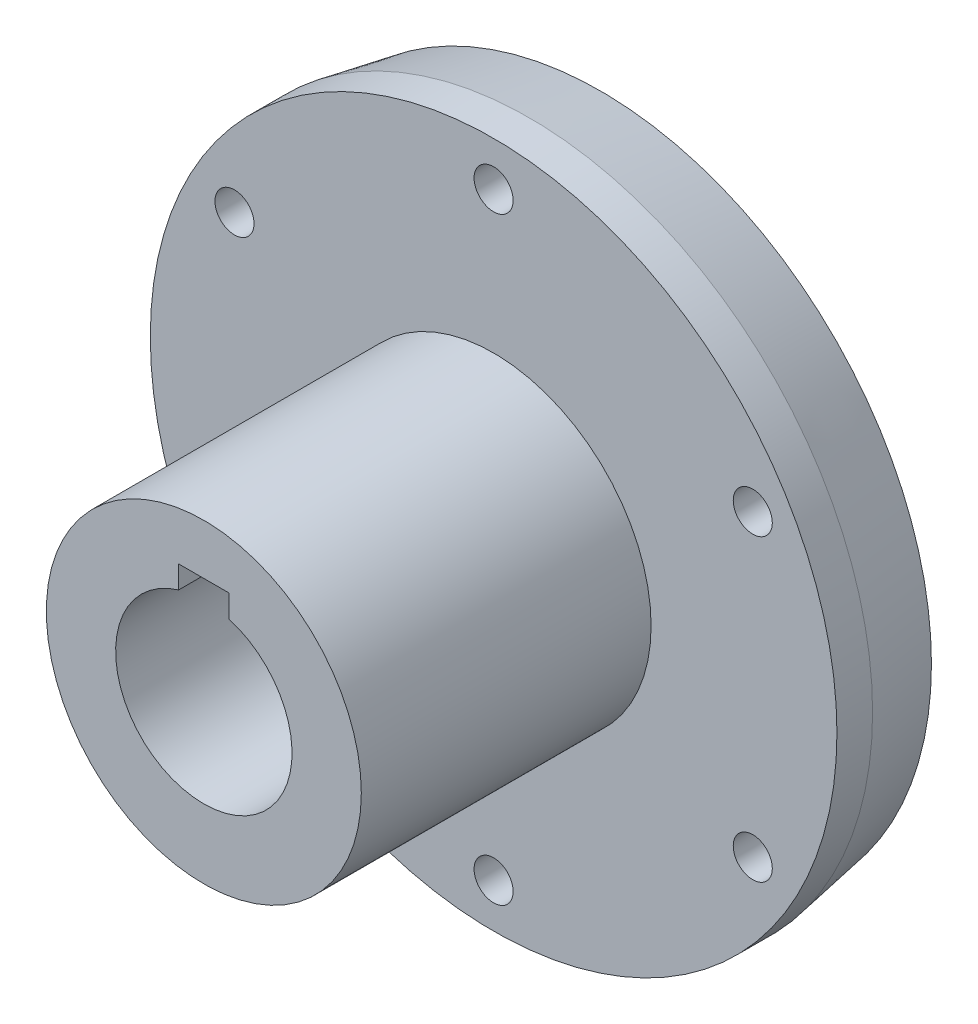
SolidWorks part; units mm, degrees
ref_plane "Plan de face" through (0, 0, 0) normal (0, 0, 1) x (1, 0, 0)
ref_plane "Plan de dessus" through (0, 0, 0) normal (0, 1, 0) x (1, 0, 0)
ref_plane "Plan de droite" through (0, 0, 0) normal (1, 0, 0) x (0, 0, -1)
sketch "Esquisse1" plane through (0, 0, 0) normal (0, 0, 1) x (1, 0, 0)
  circle A0 centre (0, 0) radius 54.5
  dimension "D1" = 109
extrude "Boss.-Extru.1" add sketch "Esquisse1" along normal blind 17
sketch "Esquisse5" plane through (0, 0, 17) normal (0, 0, 1) x (1, 0, 0)
  circle A0 centre (0, 0) radius 25
extrude "Boss.-Extru.4" add sketch "Esquisse5" along normal blind 46
sketch "Esquisse7" plane through (0, 0, 63) normal (0, 0, 1) x (1, 0, 0)
  line L0 (-4, 13.4164) -> (-4, 17)
  line L1 (-4, 17) -> (4, 17)
  line L2 (4, 17) -> (4, 13.4164)
  line L3 (0, 0) -> (0, 14) construction
  circle A0 centre (0, 0) radius 14
  dimension "D1" = 8
  dimension "D4" = 28
  dimension "D2" = 4
  dimension "D3" = 17
extrude "Enlèv. mat.-Extru.2" cut sketch "Esquisse7" against normal blind 56
sketch "Esquisse8" plane through (0, 0, 0) normal (0, 0, -1) x (-1, 0, 0)
  circle A0 centre (0, 0) radius 5.1
  dimension "D1" = 10.2
extrude "Enlèv. mat.-Extru.3" cut sketch "Esquisse8" against normal blind 76
sketch "Esquisse9" plane through (0, 0, 0) normal (0, 0, -1) x (-1, 0, 0)
  circle A0 centre (0, 47.5) radius 3.1
  circle A2 centre (0, 0) radius 47.5
  circle A3 centre (41.1362, 23.75) radius 3.1
  circle A4 centre (41.1362, -23.75) radius 3.1
  circle A5 centre (0, -47.5) radius 3.1
  circle A6 centre (-41.1362, -23.75) radius 3.1
  circle A7 centre (-41.1362, 23.75) radius 3.1
  point P18 (0, 0)
  dimension "D1" = 6.2
  dimension "D3" = 95
  dimension "D2" = 6
extrude "Enlèv. mat.-Extru.4" cut sketch "Esquisse9" against normal blind 76 contours A2 A3 | A2 A3 | A0 A2 | A2 A0 | A2 A4 | A2 A4 | A2 A5 | A2 A6 | A2 A6 | A2 A7 | A2 A7
chamfer "Chanfrein1" distance 2 angle 80 1 edges at (54.5, 0, 0)
